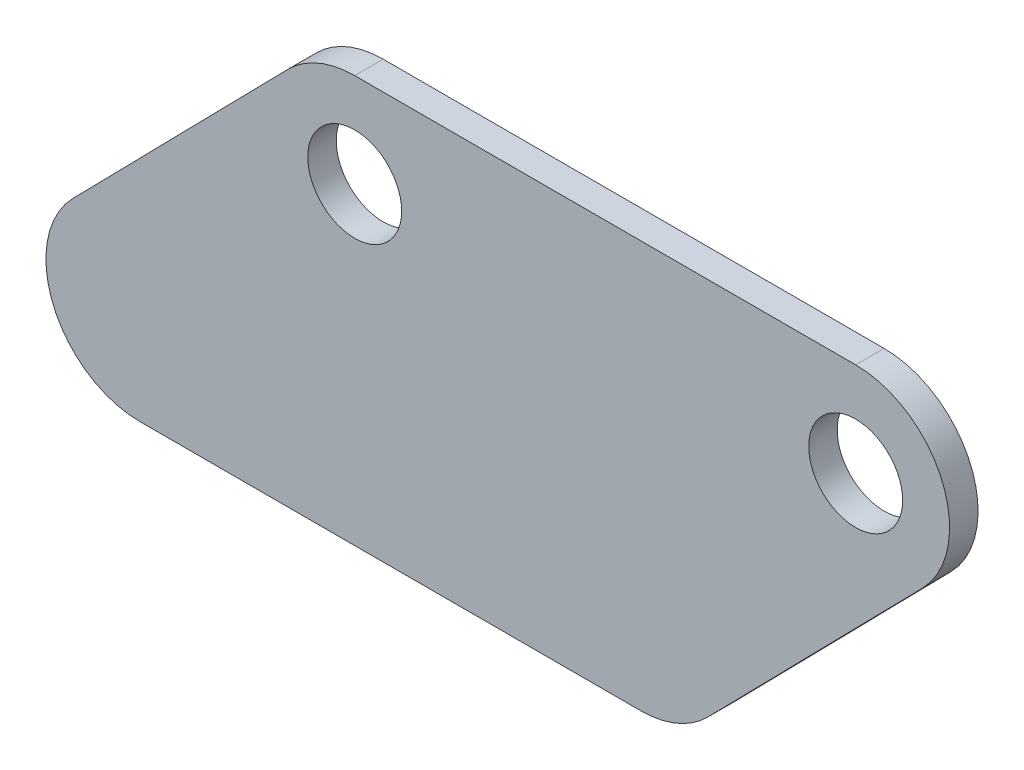
SolidWorks part; units mm, degrees
ref_plane "Front Plane" through (0, 0, 0) normal (0, 0, 1) x (1, 0, 0)
ref_plane "Top Plane" through (0, 0, 0) normal (0, 1, 0) x (1, 0, 0)
ref_plane "Right Plane" through (0, 0, 0) normal (1, 0, 0) x (0, 0, -1)
sketch "Sketch1" plane through (0, 0, 0) normal (0, 0, 1) x (1, 0, 0)
  line L0 (69.6182, -7.3343) -> (36.2557, -41.3709)
  line L1 (-1.2266, 7.3342) -> (-25.19, -17.1133)
  line L2 (0, -34.925) -> (39.7608, -34.925)
  line L4 (6.2558, 0) -> (62.1358, 0)
  line L5 (0, -34.925) -> (-33.9767, -34.925)
  line L6 (6.2558, 10.4775) -> (62.1358, 10.4775)
  line L7 (0, -34.925) -> (83.5815, -34.925) construction
  circle A2 centre (6.2558, 0) radius 5.2388
  circle A3 centre (62.1358, 0) radius 5.2388
  circle A4 centre (-17.7075, -24.4475) radius 10.4775
  circle A6 centre (62.1358, -34.925) radius 13.97
  circle A7 centre (62.1358, 0) radius 10.4775
  circle A8 centre (6.2558, 0) radius 10.4775
  circle A9 centre (38.1725, -24.4475) radius 10.4775
  dimension "D1" = 34.925
extrude "Boss-Extrude1" add sketch "Sketch1" along normal blind 3.175
